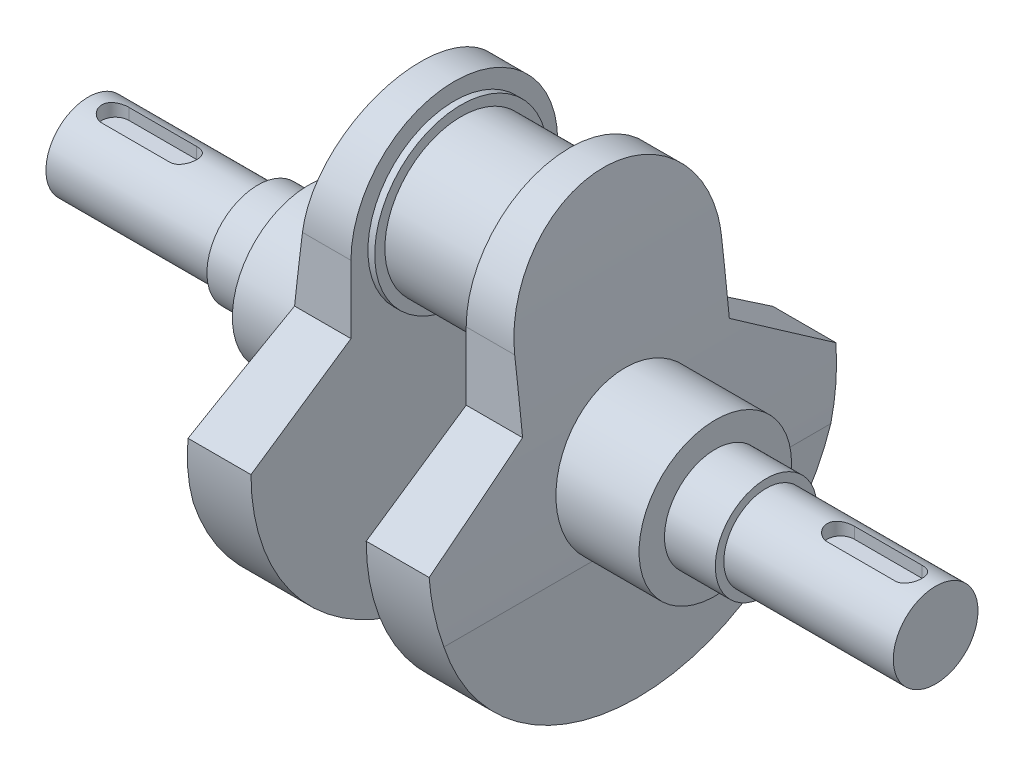
SolidWorks part; units mm, degrees
ref_plane "Front Plane" through (0, 0, 0) normal (0, 0, 1) x (1, 0, 0)
ref_plane "Top Plane" through (0, 0, 0) normal (0, 1, 0) x (1, 0, 0)
ref_plane "Right Plane" through (0, 0, 0) normal (1, 0, 0) x (0, 0, -1)
sketch "Sketch1" plane through (0, 0, 0) normal (1, 0, 0) x (0, 0, -1)
  circle A0 centre (0, 0) radius 22.5
  dimension "D1" = 45
extrude "Boss-Extrude1" add sketch "Sketch1" along normal mid plane 30
sketch "Sketch2" plane through (15, 0, 0) normal (1, 0, 0) x (0, 0, -1)
  circle A2 centre (0, 0) radius 25.5
  circle A3 centre (0, 0) radius 25.5
  dimension "D1" = 3
extrude "Boss-Extrude2" add sketch "Sketch2" along normal blind 2
sketch "Sketch3" plane through (17, 0, 0) normal (1, 0, 0) x (0, 0, -1)
  line L0 (-30.5, 0) -> (-30.5, -20)
  line L1 (-30.5, -20) -> (-60, -40)
  line L2 (0, 0) -> (0, -40) construction
  line L3 (30.5, -20) -> (60, -40)
  line L4 (30.5, 0) -> (30.5, -20)
  arc A1 (-60, -40) -> (60, -40) centre (0, -40) ccw
  circle A2 centre (0, 0) radius 30.5
  arc A3 (30.5, 0) -> (-30.5, 0) centre (0, 0) ccw
  dimension "D2" = 120
  dimension "D3" = 40
  dimension "D4" = 20
  dimension "D1" = 5
extrude "Boss-Extrude3" add sketch "Sketch3" along normal blind 20
sketch "Sketch4" plane through (0, 0, 0) normal (0, 0, 1) x (1, 0, 0)
  line L0 (27, 30.5) -> (37, 30.5)
  line L1 (37, 30.5) -> (17, 30.5) construction
  line L2 (37, 30.5) -> (37, -58.5)
  line L3 (37, -20) -> (37, -40) construction
  arc A0 (27, 30.5) -> (37, -58.5) centre (-995.0675, -129.4008) cw
  dimension "D3" = 1034.5
  dimension "D1" = 10
  dimension "D2" = 89
extrude "Cut-Extrude1" cut sketch "Sketch4" against normal mid plane 198
ref_plane "Plane1" through (60, 0, 0) normal (1, 0, 0) x (0, 0, -1)
sketch "Sketch5" plane through (60, 0, 0) normal (1, 0, 0) x (0, 0, -1)
  circle A0 centre (0, -40) radius 22.5
  point P2 (0, 0)
  dimension "D1" = 45
  dimension "D2" = 40
extrude "Boss-Extrude4" add sketch "Sketch5" against normal up to body
sketch "Sketch6" plane through (60, 0, 0) normal (1, 0, 0) x (0, 0, -1)
  circle A0 centre (0, -40) radius 15
  dimension "D1" = 30
extrude "Boss-Extrude5" add sketch "Sketch6" along normal blind 15
sketch "Sketch7" plane through (75, 0, 0) normal (1, 0, 0) x (0, 0, -1)
  circle A0 centre (0, -40) radius 12.5
  dimension "D1" = 25
extrude "Boss-Extrude6" add sketch "Sketch7" along normal blind 50
ref_plane "Plane2" through (0, 27.5, 0) normal (0, 1, 0) x (1, 0, 0)
ref_plane "Plane3" through (0, -27.5, 0) normal (0, 1, 0) x (-1, 0, 0)
sketch "Sketch9" plane through (0, -27.5, 0) normal (0, 1, 0) x (-1, 0, 0)
  line L0 (-125, 0) -> (-85.2742, 0) construction
  line L1 (-125, 12.5) -> (-125, -12.5) construction
  line L2 (-97, 0) -> (-117, 0) construction
  line L3 (-97, -4) -> (-117, -4)
  line L4 (-97, 4) -> (-117, 4)
  arc A0 (-97, -4) -> (-97, 4) centre (-97, 0) ccw
  arc A1 (-117, 4) -> (-117, -4) centre (-117, 0) ccw
  point P7 (-107, 0)
  dimension "D3" = 4
  dimension "D1" = 8
  dimension "D2" = 20
extrude "Cut-Extrude2" cut sketch "Sketch9" against normal blind 4
mirror "Mirror2" about plane through (0, 0, 0) normal (1, 0, 0) of bodies 108
